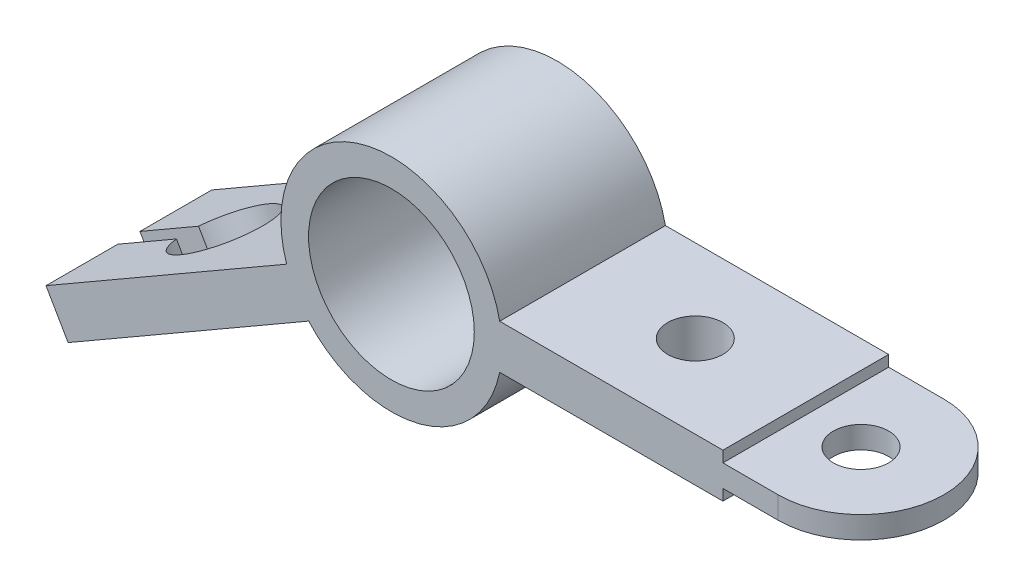
SolidWorks part; units mm, degrees
ref_plane "Ön Düzlem" through (0, 0, 0) normal (0, 0, 1) x (1, 0, 0)
ref_plane "Üst Düzlem" through (0, 0, 0) normal (0, 1, 0) x (1, 0, 0)
ref_plane "Sağ Düzlem" through (0, 0, 0) normal (1, 0, 0) x (0, 0, -1)
sketch "Çizim1" plane through (0, 0, 0) normal (0, 0, 1) x (1, 0, 0)
  line L0 (0, 0) -> (-85.8597, 0) construction
  line L1 (0, 0) -> (-145.292, -83.8843) construction
  line L2 (-146.3068, -96.0173) -> (-156.3068, -78.6968)
  line L3 (-156.3068, -78.6968) -> (-47.4264, -15.8346)
  line L4 (-146.3068, -96.0173) -> (-37.4264, -33.1552)
  line L5 (0, 0) -> (272.6102, 0) construction
  line L6 (150, -10) -> (150, 10)
  line L7 (150, 10) -> (48.9898, 10)
  line L8 (150, -10) -> (48.9898, -10)
  line L9 (150, 5) -> (175, 5)
  line L10 (175, 5) -> (175, -5)
  line L11 (150, -5) -> (175, -5)
  circle A0 centre (0, 0) radius 50
  circle A1 centre (0, 0) radius 37.5
  point P11 (-151.3068, -87.357)
  point P17 (150, 0)
  point P21 (175, 0)
  dimension "D1" = 75
  dimension "D2" = 100
  dimension "D3" = 30
  dimension "D4" = 10
  dimension "D5" = 175
  dimension "D6" = 10
  dimension "D7" = 150
  dimension "D8" = 5
  dimension "D9" = 25
extrude "Yükseklik-Ekstrüzyon1" add sketch "Çizim1" along normal mid plane 75 contours A0 L3 L2 L4 | A0 A1 | A0 L8 L6 L7 | L6 L11 L10 L9
sketch "Çizim2" plane through (0, 5, 0) normal (0, 1, 0) x (1, 0, 0)
  line L0 (175, -37.5) -> (175, 37.5) construction
  line L2 (175, 37.5) -> (175, -37.5)
  arc A0 (175, 37.5) -> (175, -37.5) centre (175, 0) cw
extrude "Yükseklik-Ekstrüzyon2" add sketch "Çizim2" against normal blind 10
sketch "Çizim3" plane through (0, 5, 0) normal (0, 1, 0) x (1, 0, 0)
  circle A0 centre (175, 0) radius 12.5
  dimension "D1" = 25
extrude "Kes-Ekstrüzyon1" cut sketch "Çizim3" against normal blind 10
sketch "Çizim4" plane through (0, 10, 0) normal (0, 1, 0) x (1, 0, 0)
  line L0 (150, -37.5) -> (150, 37.5) construction
  line L1 (150, -37.5) -> (48.9898, -37.5) construction
  circle A0 centre (100, 0) radius 12.5
  point P2 (0, 0)
  point P3 (0, 0)
  dimension "D1" = 25
  dimension "D2" = 50
  dimension "D3" = 37.5
extrude "Kes-Ekstrüzyon2" cut sketch "Çizim4" against normal through all
sketch "Çizim5" plane through (-5, 8.6603, 0) normal (-0.5, 0.866, 0) x (0.866, 0.5, 0)
  line L0 (-174.7141, 5) -> (-174.7141, -5)
  line L1 (-174.7141, -37.5) -> (-174.7141, 37.5) construction
  line L2 (-174.7141, -5) -> (-144.079, -5)
  line L3 (-174.7141, 5) -> (-144.079, 5)
  line L4 (-174.7141, 37.5) -> (-48.9898, 37.5) construction
  line L5 (-174.7141, -37.5) -> (-48.9898, -37.5) construction
  arc A0 (-144.079, -5) -> (-144.079, 5) centre (-124.7141, 0) ccw
  point P10 (-174.7141, 2.3099)
  point P11 (0, 0)
  point P12 (0, 0)
  dimension "D3" = 40
  dimension "D1" = 10
  dimension "D2" = 32.5
  dimension "D4" = 50
  dimension "D5" = 37.5
extrude "Kes-Ekstrüzyon3" cut sketch "Çizim5" against normal through all contours A0 L3 L0 L2
